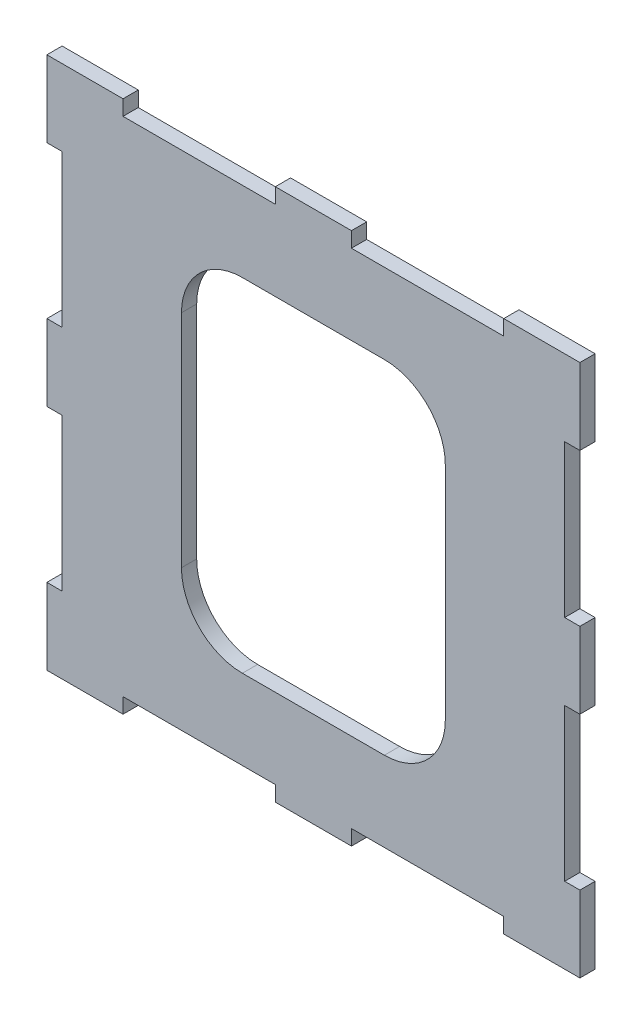
SolidWorks part; units mm, degrees
ref_plane "Front Plane" through (0, 0, 0) normal (0, 0, 1) x (1, 0, 0)
ref_plane "Top Plane" through (0, 0, 0) normal (0, 1, 0) x (1, 0, 0)
ref_plane "Right Plane" through (0, 0, 0) normal (1, 0, 0) x (0, 0, -1)
sketch "Sketch1" plane through (0, 0, 0) normal (0, 0, 1) x (1, 0, 0)
  line L1 (-35, -35) -> (35, -35)
  line L2 (-35, -35) -> (-35, 35)
  line L3 (-35, 35) -> (35, 35)
  line L4 (35, -35) -> (35, 35)
  line L5 (0, 35) -> (0, -35) construction
  line L6 (-35, 0) -> (35, 0) construction
  line L11 (0, 18) -> (0, -18) construction
  line L12 (-17.25, 0) -> (17.25, 0) construction
  point P0 (0, 0)
  point P4 (0, 0)
  dimension "D1" = 70
  dimension "D2" = 70
extrude "Boss-Extrude1" add sketch "Sketch1" against normal blind 2
sketch "Sketch2" plane through (0, 0, 0) normal (0, 0, 1) x (1, 0, 0)
  line L0 (-35, 35) -> (-25, 35)
  line L1 (35, 35) -> (-35, 35) construction
  line L2 (-25, 35) -> (-5, 35)
  line L3 (-5, 35) -> (5, 35)
  line L4 (5, 35) -> (25, 35)
  line L6 (35, 35) -> (35, 25)
  line L7 (-25, 33) -> (-5, 33)
  line L8 (-25, 33) -> (-25, 37)
  line L9 (-25, 37) -> (-5, 37)
  line L10 (-5, 33) -> (-5, 37)
  line L11 (-15, 37) -> (-15, 33) construction
  line L12 (-25, 35) -> (-5, 35) construction
  line L13 (5, 33) -> (25, 33)
  line L14 (5, 33) -> (5, 37)
  line L15 (5, 37) -> (25, 37)
  line L16 (25, 33) -> (25, 37)
  line L17 (15, 37) -> (15, 33) construction
  line L18 (5, 35) -> (25, 35) construction
  line L19 (35, -35) -> (35, 35) construction
  line L20 (35, 25) -> (35, 5)
  line L21 (35, 5) -> (35, -5)
  line L22 (35, -5) -> (35, -25)
  line L23 (-35, -35) -> (-25, -35)
  line L24 (35, -5) -> (33, -5)
  line L25 (35, -5) -> (35, -25)
  line L26 (35, -25) -> (33, -25)
  line L27 (33, -5) -> (33, -25)
  line L28 (35, 25) -> (33, 25)
  line L29 (35, 25) -> (35, 5)
  line L30 (35, 5) -> (33, 5)
  line L31 (33, 25) -> (33, 5)
  line L32 (-35, -35) -> (35, -35) construction
  line L33 (-25, -35) -> (-5, -35)
  line L34 (-5, -35) -> (5, -35)
  line L35 (5, -35) -> (25, -35)
  line L36 (-35, 35) -> (-35, 25)
  line L37 (-25, -35) -> (-5, -35)
  line L38 (-25, -35) -> (-25, -33)
  line L39 (-25, -33) -> (-5, -33)
  line L40 (-5, -35) -> (-5, -33)
  line L41 (5, -35) -> (25, -35)
  line L42 (5, -35) -> (5, -33)
  line L43 (5, -33) -> (25, -33)
  line L44 (25, -35) -> (25, -33)
  line L45 (-35, 35) -> (-35, -35) construction
  line L46 (-35, 25) -> (-35, 5)
  line L47 (-35, 5) -> (-35, -5)
  line L48 (-35, -5) -> (-35, -25)
  line L50 (-35, 25) -> (-33, 25)
  line L51 (-35, 25) -> (-35, 5)
  line L52 (-35, 5) -> (-33, 5)
  line L53 (-33, 25) -> (-33, 5)
  line L54 (-35, -5) -> (-33, -5)
  line L55 (-35, -5) -> (-35, -25)
  line L56 (-35, -25) -> (-33, -25)
  line L57 (-33, -5) -> (-33, -25)
  point P7 (15, 35)
  point P9 (-15, 35)
  point P10 (-15, 35)
  point P14 (15, 35)
  line M25 (35, -35) -> (35, 35)
  line M26 (35, 35) -> (-35, 35)
  line M27 (-35, 35) -> (-35, -35)
  line M28 (-35, -35) -> (35, -35)
  dimension "D1" = 10
  dimension "D2" = 20
  dimension "D3" = 10
  dimension "D4" = 20
  dimension "D5" = 4
  dimension "D6" = 20
  dimension "D7" = 20
  dimension "D8" = 4
  dimension "D9" = 10
  dimension "D10" = 20
  dimension "D11" = 10
  dimension "D12" = 20
  dimension "D13" = 2
  dimension "D14" = 2
  dimension "D15" = 10
  dimension "D16" = 20
  dimension "D17" = 10
  dimension "D18" = 20
  dimension "D19" = 20
  dimension "D20" = 20
  dimension "D21" = 2
  dimension "D22" = 2
  dimension "D23" = 10
  dimension "D24" = 20
  dimension "D25" = 10
  dimension "D26" = 20
  dimension "D27" = 2
  dimension "D28" = 2
extrude "Cut-Extrude1" cut sketch "Sketch2" against normal blind 2 contours L53 L50 L52 M27 | L57 L54 L56 M27 | L40 L39 L38 M28 | L44 L43 L42 M28 | L24 L27 L26 M25 | L28 L31 L30 M25 | L13 L16 L14 M26 | L7 L10 L8 M26
sketch "Sketch6" plane through (0, 0, -2) normal (0, 0, -1) x (-1, 0, 0)
  line L1 (-17.325, -22.5) -> (17.325, -22.5)
  line L2 (-17.325, -22.5) -> (-17.325, 22.5)
  line L3 (-17.325, 22.5) -> (17.325, 22.5)
  line L4 (17.325, -22.5) -> (17.325, 22.5)
  line L5 (0, 22.5) -> (0, -22.5) construction
  line L6 (-17.325, 0) -> (17.325, 0) construction
  line L7 (-17.325, -22.5) -> (-9.325, -22.5)
  line L8 (-17.325, -22.5) -> (-17.325, -14.5)
  line L9 (-17.325, -14.5) -> (-9.325, -14.5)
  line L10 (-9.325, -22.5) -> (-9.325, -14.5)
  line L11 (17.325, -22.5) -> (9.325, -22.5)
  line L12 (17.325, -22.5) -> (17.325, -14.5)
  line L13 (17.325, -14.5) -> (9.325, -14.5)
  line L14 (9.325, -22.5) -> (9.325, -14.5)
  line L15 (-17.325, 22.5) -> (-9.325, 22.5)
  line L16 (-17.325, 22.5) -> (-17.325, 14.5)
  line L17 (-17.325, 14.5) -> (-9.325, 14.5)
  line L18 (-9.325, 22.5) -> (-9.325, 14.5)
  line L19 (17.325, 22.5) -> (9.325, 22.5)
  line L20 (17.325, 22.5) -> (17.325, 14.5)
  line L21 (17.325, 14.5) -> (9.325, 14.5)
  line L22 (9.325, 22.5) -> (9.325, 14.5)
  arc A0 (-9.325, 22.5) -> (-17.325, 14.5) centre (-9.325, 14.5) ccw
  arc A1 (9.325, 22.5) -> (17.325, 14.5) centre (9.325, 14.5) cw
  arc A2 (-9.325, -22.5) -> (-17.325, -14.5) centre (-9.325, -14.5) cw
  arc A3 (9.325, -22.5) -> (17.325, -14.5) centre (9.325, -14.5) ccw
  point P0 (0, 0)
  dimension "D1" = 34.65
  dimension "D2" = 45
  dimension "D3" = 8
  dimension "D4" = 8
  dimension "D5" = 8
  dimension "D6" = 8
  dimension "D7" = 8
  dimension "D8" = 8
  dimension "D9" = 8
  dimension "D10" = 8
extrude "Cut-Extrude2" cut sketch "Sketch6" against normal blind 10 contours L22 L3 L18 L17 L2 L9 L10 L1 L14 L13 L4 L21 | L18 A0 L17 | A1 L22 L21 | A2 L10 L9 | L14 A3 L13
